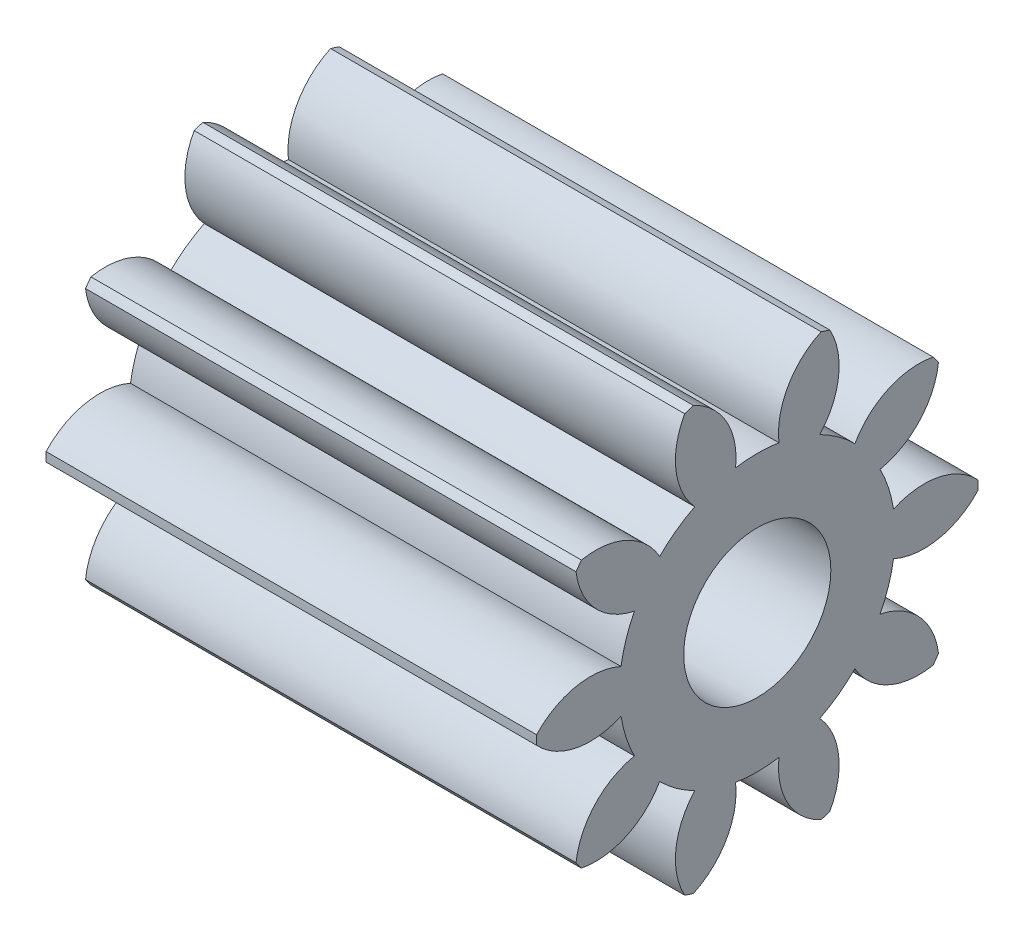
SolidWorks part; units mm, degrees
ref_plane "Plane1" through (0, 0, 0) normal (0, 0, 1) x (1, 0, 0)
ref_plane "Plane2" through (0, 0, 0) normal (0, 1, 0) x (1, 0, 0)
ref_plane "Plane3" through (0, 0, 0) normal (1, 0, 0) x (0, 0, -1)
sketch "HoldingSke" plane through (0, 0, 0) normal (0, 1, 0) x (1, 0, 0)
  line L0 (0, 0) -> (0.6565, -0.1158)
  line L1 (-15, 0) -> (100, 0) construction
  line L2 (0, 0) -> (-2.1039, 2.3779)
  line L3 (0, 0) -> (-11.863, 4.5341)
  line L4 (0, 0) -> (8.5048, 1.4996)
  line L5 (0, 0) -> (-46.8476, -17.4728)
  line L6 (0, 0) -> (-16.5793, -11.1861)
  line L7 (-2.1039, 2.3779) -> (8.6586, 51.2059)
  line L8 (-76.2, 54.61) -> (-75.3, 54.61)
  line L9 (-71.009, 38.7566) -> (-53.1078, 45.2721)
  line L10 (-76.2, 71.12) -> (104.1128, 71.12)
  line L11 (0, 0) -> (-20, 0)
  line L12 (-76.2, 101.6) -> (-76.147, 101.6)
  line L13 (24.9733, 27.94) -> (52.9518, 28.4284)
  line L14 (24.9733, 27.94) -> (24.9743, 27.94)
  line L15 (24.9733, 27.94) -> (100.4006, 29.5858)
  line L16 (-63.627, -1.5) -> (-12.827, -1.5)
  circle A0 centre (0, 0) radius 2.5
  circle A1 centre (0, 0) radius 5.624
  circle A2 centre (0, 0) radius 37.5
  circle A3 centre (0, 0) radius 2.5
  dimension "MHD" = 11.248
  dimension "Hub_dia" = 75
  dimension "Bore" = 5
  dimension "MBD" = 5
  dimension "Num_teeth" = 10
  dimension "Pitch" = 0.6667
  dimension "Overall_len" = 50
  dimension "Show_teeth" = 10
  dimension "Thickness" = 20
  dimension "OAL" = 50.0001
  dimension "T_dim" = 0.9
  dimension "Ap" = 20
  dimension "H" = 19.05
  dimension "Pitch_radius" = 180.3128
  dimension "Width" = 20
  dimension "Backlash" = 0.053
  dimension "Addendum_fac" = 1
  dimension "Dedendum_fac" = 1.25
  dimension "Clearance_fac" = 0.25
  dimension "Dedendum_add" = 0.001
  dimension "Module" = 1.5
sketch "BasProSke" plane through (0, 0, 0) normal (0, 1, 0) x (1, 0, 0)
  line L0 (-10, 0) -> (60, 0) construction
  line L1 (0, 0) -> (0, 9)
  line L2 (0, 0) -> (20, 0)
  line L3 (20, 0) -> (20, 9)
  line L4 (20, 9) -> (0, 9)
  dimension "Thickness" = 20
  dimension "Diameter" = 18
revolve "Base-Revolve" add sketch "BasProSke" angle 360 about L0
sketch "TooCutSke" plane through (0, 0, 0) normal (1, 0, 0) x (0, 0, -1)
  line L1 (0, 0) -> (0, 107) construction
  line L2 (0, 0) -> (-1.2658, 7.3924) construction
  line L3 (0, 0) -> (-4.5869, 14.117) construction
  line L4 (-1.2658, 7.3924) -> (-2.2934, 7.0585) construction
  arc A0 (0.8839, 5.5541) -> (-0.8839, 5.5541) centre (0, 0) ccw
  arc A1 (2.6378, 8.6313) -> (-2.6378, 8.6313) centre (0, 0) ccw
  circle A2 centre (0, 0) radius 7.5 construction
  circle A3 centre (0, 0) radius 7.0477 construction
  arc A4 (-0.8839, 5.5541) -> (-2.6378, 8.6313) centre (-3.8646, 5.8936) ccw
  arc A5 (2.6378, 8.6313) -> (0.8839, 5.5541) centre (3.8646, 5.8936) ccw
  dimension "Root_dia" = 11.248
  dimension "Overcut_dia" = 18.0508
  dimension "Pitch_dia" = 15
  dimension "Base_dia" = 14.0954
  dimension "Flank_rad" = 3
  dimension "Half_ang" = 18
  dimension "Half_CT" = 1.0805
extrude "ToothCut" cut sketch "TooCutSke" along normal through all
fillet "Breaks" [suppressed] radius 0.03
fillet "RootFillets" [suppressed] radius 0.376
pattern_circular "TeethCuts" count 10 every 36 about axis through (-10, 0, 0) along (1, 0, 0) of "ToothCut", "RootFillets", "Breaks"
sketch "HubNeaOneSke" plane through (0, 0, 0) normal (-1, 0, 0) x (0, 0, 1)
  circle A0 centre (0, 0) radius 5.624
  dimension "Diameter" = 11.248
extrude "HubNearOne" [suppressed] add sketch "HubNeaOneSke" along normal blind 30.0001
sketch "HubNeaBotSke" plane through (0, 0, 0) normal (-1, 0, 0) x (0, 0, 1)
  circle A0 centre (0, 0) radius 5.624
  dimension "Diameter" = 11.248
extrude "HubNearBoth" [suppressed] add sketch "HubNeaBotSke" along normal blind 15
ref_plane "FarPln" through (20, 0, 0) normal (1, 0, 0) x (0, 0, -1)
sketch "HubFarSke" plane through (20, 0, 0) normal (1, 0, 0) x (0, 0, -1)
  circle A0 centre (0, 0) radius 5.624
  dimension "Diameter" = 11.248
extrude "HubFar" [suppressed] add sketch "HubFarSke" along normal blind 15
sketch "BorSke" plane through (0, 0, 0) normal (1, 0, 0) x (0, 0, -1)
  circle A0 centre (0, 0) radius 2.5
  dimension "Diameter" = 5
extrude "Bore" cut sketch "BorSke" along normal mid plane 100.0001
sketch "KeySke" plane through (0, 0, 0) normal (1, 0, 0) x (0, 0, -1)
  line L0 (-1, 0) -> (-1, 3.4)
  line L1 (-1, 3.4) -> (1, 3.4)
  line L2 (1, 3.4) -> (1, 0)
  line L3 (0, 0) -> (0, 34) construction
  line L4 (-1, 0) -> (1, 0)
  dimension "Offset" = 3.4
extrude "Keyway" [suppressed] cut sketch "KeySke" along normal mid plane 100.0001
pattern_circular "Keyway2" [suppressed] count 2 every 90 about axis through (-10, 0, 0) along (1, 0, 0)
sketch "Çizim1" plane through (20, 0, 0) normal (1, 0, 0) x (0, 0, -1)
  circle A1 centre (0, 0) radius 3
  dimension "D1" = 6
extrude "Kes-Ekstrüzyon1" cut sketch "Çizim1" against normal blind 26
equation "' \"Module@HoldingSke\" = 6.35"
equation "' \"Num_teeth@HoldingSke\" = 12"
equation "' \"Ap@HoldingSke\" =  20"
equation "' \"Ap@HoldingSke\" = 20"
equation "' \"Width@HoldingSke\" = 0.5 * 25.4"
equation "' \"Hub_dia@HoldingSke\"= 1 * 25.4"
equation "' \"Hub_dia@HoldingSke\" = 1 * 25.4"
equation "' \"Overall_len@HoldingSke\" = 1.0 * 25.4"
equation "' \"Bore@HoldingSke\" = 0.75 * 25.4"
equation "' \"T_dim@HoldingSke\" = 0.1 * 25.4"
equation "' \"Width@KeySke\" = 0.25 * 25.4"
equation "' \"Show_teeth@HoldingSke\" = 13"
equation "' \"Backlash@HoldingSke\" = 0.009 * 25.4"
equation "' \"Addendum_fac@HoldingSke\" = 1.0"
equation "' \"Dedendum_fac@HoldingSke\" = 1.25"
equation "' \"Dedendum_add@HoldingSke\" = 0.00005 * 25.4"
equation "' \"Clearance_fac@HoldingSke\" = 0.25"
equation "\"Pitch@HoldingSke\" = 1 / \"Module@HoldingSke\""
equation "\"Overcut_dia@TooCutSke\" = (\"Num_teeth@HoldingSke\" + 2 * \"Addendum_fac@HoldingSke\") / \"Pitch@HoldingSke\" + 0.002 * 25.4"
equation "\"Pitch_dia@TooCutSke\" = \"Num_teeth@HoldingSke\" / \"Pitch@HoldingSke\""
equation "\"Base_dia@TooCutSke\" = \"Num_teeth@HoldingSke\" / \"Pitch@HoldingSke\" * cos((\"Ap@HoldingSke\"  * 3.14159265 / 180))"
equation "\"Root_dia@TooCutSke\" = (\"Num_teeth@HoldingSke\" + 2) / \"Pitch@HoldingSke\" - 2 * (\"Addendum_fac@HoldingSke\" + \"Dedendum_fac@HoldingSke\") / \"Pitch@HoldingSke\" - \"Dedendum_add@HoldingSke\" * 2"
equation "\"Half_ang@TooCutSke\" = 180 / \"Num_teeth@HoldingSke\""
equation "\"Half_CT@TooCutSke\" = \"Num_teeth@HoldingSke\" / \"Pitch@HoldingSke\" * sin((3.14159265 / 2 / \"Num_teeth@HoldingSke\")) / 2 - 7 * \"Backlash@HoldingSke\" / 4"
equation "\"Flank_rad@TooCutSke\" = \"Num_teeth@HoldingSke\" / \"Pitch@HoldingSke\" / 5"
equation "\"Radius@RootFillets\" = \"Clearance_fac@HoldingSke\" / \"Pitch@HoldingSke\" + \"Dedendum_add@HoldingSke\""
equation "\"Break_rad@Breaks\" = 0.02 / \"Pitch@HoldingSke\""
equation "\"Thickness@HoldingSke\" = \"Width@HoldingSke\""
equation "\"OAL@HoldingSke\" = \"Thickness@HoldingSke\""
equation "\"MHD@HoldingSke\" = (\"Num_teeth@HoldingSke\" + 2) / \"Pitch@HoldingSke\" - 2 * (\"Addendum_fac@HoldingSke\" + \"Dedendum_fac@HoldingSke\")  / \"Pitch@HoldingSke\" - \"Dedendum_add@HoldingSke\" * 2"
equation "\"MBD@HoldingSke\" = (\"Num_teeth@HoldingSke\" + 2) / \"Pitch@HoldingSke\" - 2 * (\"Addendum_fac@HoldingSke\" + \"Dedendum_fac@HoldingSke\")  / \"Pitch@HoldingSke\" - \"Dedendum_add@HoldingSke\" * 2 - 0.002 * 25.4"
equation "\"MHD@HoldingSke\" = ((sgn( \"MHD@HoldingSke\" - \"Hub_dia@HoldingSke\" )-1)*( \"MHD@HoldingSke\" - \"Hub_dia@HoldingSke\" ))/-2+ \"Hub_dia@HoldingSke\""
equation "\"MBD@HoldingSke\" = ((sgn( \"MBD@HoldingSke\" - \"Bore@HoldingSke\" )-1)*( \"MBD@HoldingSke\" - \"Bore@HoldingSke\" ))/-2+ \"Bore@HoldingSke\""
equation "\"OAL@HoldingSke\" = ((sgn( \"OAL@HoldingSke\" - \"Overall_len@HoldingSke\" )+1)*( \"OAL@HoldingSke\" - \"Overall_len@HoldingSke\" ))/2 + \"Overall_len@HoldingSke\" + 0.000002 * 25.4"
equation "\"Num_teeth@TeethCuts\" = int( \"Show_teeth@HoldingSke\" ) + 1"
equation "\"Num_teeth@TeethCuts\" = ((sgn( \"Num_teeth@TeethCuts\" - \"Num_teeth@HoldingSke\" )-1)*( \"Num_teeth@TeethCuts\" - \"Num_teeth@HoldingSke\" ))/-2+ \"Num_teeth@HoldingSke\""
equation "\"Num_teeth@TeethCuts\" = ((sgn( \"Num_teeth@TeethCuts\" - 2.0)+1)*( \"Num_teeth@TeethCuts\" - 2.0))/2 +2.0"
equation "\"Angle@TeethCuts\" = 360.0 / \"Num_teeth@HoldingSke\""
equation "\"Diameter@BasProSke\" = (\"Num_teeth@HoldingSke\" + 2 * \"Addendum_fac@HoldingSke\") / \"Pitch@HoldingSke\""
equation "\"Thickness@BasProSke\"  = \"Thickness@HoldingSke\""
equation "' \"Fillet_rad@BasProSke\" =  \"Thickness@HoldingSke\" * 0.05"
equation "' \"Fillet_rad@BasProSke\" = \"Thickness@HoldingSke\" * 0.05"
equation "\"MHD@HoldingSke\" = ((sgn( \"MHD@HoldingSke\" - \"Root_dia@TooCutSke\" )-1)*( \"MHD@HoldingSke\" - \"Root_dia@TooCutSke\" ))/-2+ \"Root_dia@TooCutSke\""
equation "\"Diameter@HubNeaOneSke\" = \"MHD@HoldingSke\""
equation "\"Length@HubNearOne\" = \"OAL@HoldingSke\" - \"Thickness@BasProSke\""
equation "\"Diameter@HubNeaBotSke\" = \"MHD@HoldingSke\""
equation "\"Length@HubNearBoth\" = ( \"OAL@HoldingSke\" - \"Thickness@BasProSke\" ) / 2.0"
equation "\"Thickness@FarPln\" = \"Thickness@BasProSke\""
equation "\"Diameter@HubFarSke\" = \"MHD@HoldingSke\""
equation "\"Length@HubFar\" = ( \"OAL@HoldingSke\" - \"Thickness@BasProSke\" ) / 2.0"
equation "\"Diameter@BorSke\" = \"MBD@HoldingSke\""
equation "\"D1@Bore\" = \"OAL@HoldingSke\" * 2.0"
equation "\"D1@Keyway\" = \"OAL@HoldingSke\" * 2.0"
equation "\"Offset@KeySke\" = \"T_dim@HoldingSke\" + \"MBD@HoldingSke\" / 2.0"
